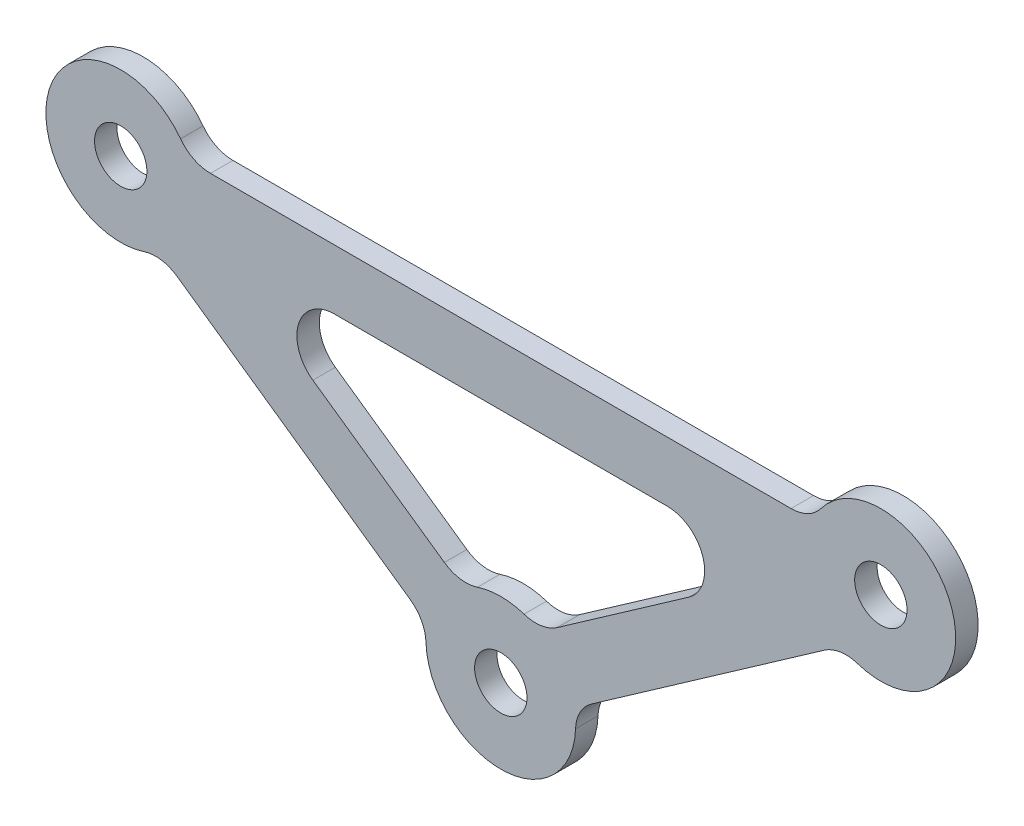
SolidWorks part; units mm, degrees
ref_plane "前基準面" through (0, 0, 0) normal (0, 0, 1) x (1, 0, 0)
ref_plane "上基準面" through (0, 0, 0) normal (0, 1, 0) x (1, 0, 0)
ref_plane "右基準面" through (0, 0, 0) normal (1, 0, 0) x (0, 0, -1)
sketch "草圖1" plane through (0, 0, 0) normal (0, 0, 1) x (1, 0, 0)
  line L0 (-22.2431, -4) -> (22.2431, -4)
  line L1 (-50.7874, 0) -> (50.7874, 0) construction
  line L2 (50.7874, 0) -> (0, -35.5617) construction
  line L3 (0, -35.5617) -> (-50.7874, 0) construction
  line L4 (25.111, -13.0958) -> (7.5355, -25.4022)
  line L5 (-7.5355, -25.4022) -> (-25.111, -13.0958)
  line L7 (43.2519, -10.1595) -> (12.1241, -31.9554)
  line L8 (-12.1241, -31.9554) -> (-43.2519, -10.1595)
  line L9 (-38.7874, 4) -> (38.7874, 4)
  line L10 (-38.101, -4) -> (38.101, -4) construction
  line L11 (-63.4738, 4) -> (63.4738, 4) construction
  line L12 (0, -40.4448) -> (-63.4738, 4) construction
  line L13 (63.4738, 4) -> (0, -40.4448) construction
  line L14 (0, -30.6786) -> (-38.101, -4) construction
  line L15 (38.101, -4) -> (0, -30.6786) construction
  circle A14 centre (50.7874, 0) radius 3.5
  circle A15 centre (-50.7874, 0) radius 3.5
  circle A16 centre (0, -35.5617) radius 3.5
  arc A17 (-42.7874, 6) -> (-47.6757, -9.5035) centre (-50.7874, 0) ccw
  arc A18 (47.6757, -9.5035) -> (42.7874, 6) centre (50.7874, 0) ccw
  arc A19 (-9.9947, -35.888) -> (9.9947, -35.888) centre (0, -35.5617) ccw
  arc A20 (3.1118, -26.0582) -> (-3.1118, -26.0582) centre (0, -35.5617) ccw
  arc A21 (38.7874, 4) -> (42.7874, 6) centre (38.7874, 9) ccw
  arc A22 (43.2519, -10.1595) -> (47.6757, -9.5035) centre (46.1198, -14.2553) cw
  arc A23 (7.5355, -25.4022) -> (3.1118, -26.0582) centre (4.6676, -21.3065) cw
  arc A24 (-7.5355, -25.4022) -> (-3.1118, -26.0582) centre (-4.6676, -21.3065) ccw
  arc A25 (-12.1241, -31.9554) -> (-9.9947, -35.888) centre (-14.992, -36.0512) cw
  arc A26 (-43.2519, -10.1595) -> (-47.6757, -9.5035) centre (-46.1198, -14.2553) ccw
  arc A27 (-38.7874, 4) -> (-42.7874, 6) centre (-38.7874, 9) cw
  arc A28 (12.1241, -31.9554) -> (9.9947, -35.888) centre (14.992, -36.0512) ccw
  arc A29 (22.2431, -4) -> (25.111, -13.0958) centre (22.2431, -9) cw
  arc A30 (-22.2431, -4) -> (-25.111, -13.0958) centre (-22.2431, -9) ccw
  point P26 (5.2133, -27.0282)
  dimension "D1" = 35
  dimension "D4" = 4
  dimension "D6" = 5
  dimension "D7" = 5
  dimension "D8" = 5
  dimension "D2" = 35
  dimension "D3" = 62
  dimension "D5" = 4
extrude "填料-伸長2" add sketch "草圖1" along normal blind 3
